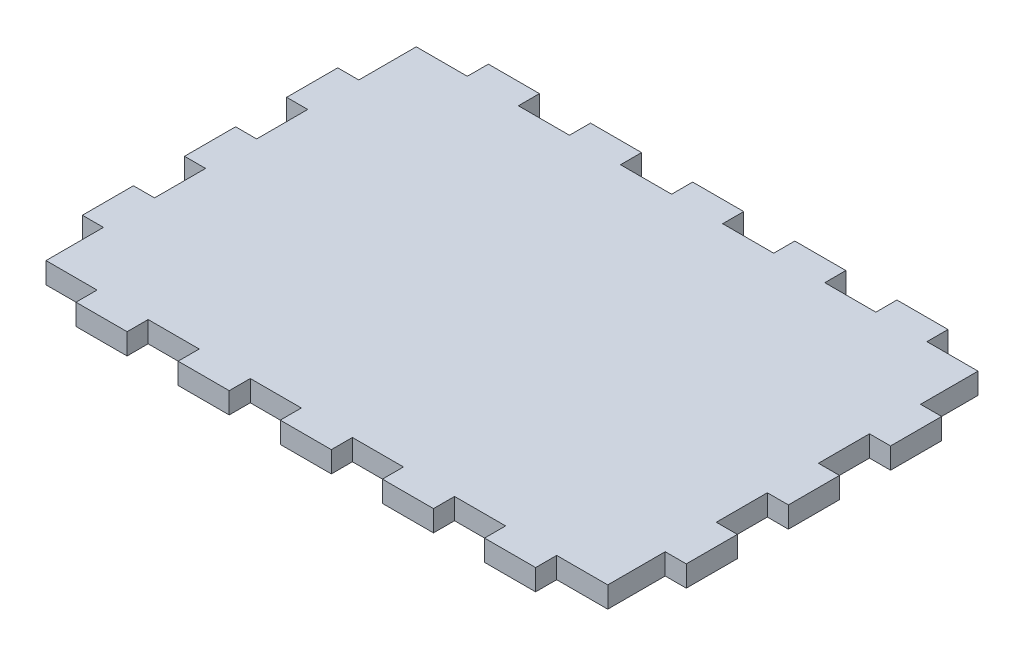
SolidWorks part; units mm, degrees
ref_plane "Plan de face" through (0, 0, 0) normal (0, 0, 1) x (1, 0, 0)
ref_plane "Plan de dessus" through (0, 0, 0) normal (0, 1, 0) x (1, 0, 0)
ref_plane "Plan de droite" through (0, 0, 0) normal (1, 0, 0) x (0, 0, -1)
sketch "Esquisse4" plane through (0, 0, 0) normal (0, 1, 0) x (1, 0, 0)
  line L1 (-44, 29) -> (44, 29)
  line L2 (-44, 29) -> (-44, -29)
  line L3 (-44, -29) -> (44, -29)
  line L4 (44, 29) -> (44, -29)
  line L5 (-44, 29) -> (44, -29) construction
  line L6 (-44, -29) -> (44, 29) construction
  point P0 (0, 0)
  dimension "D1" = 58
  dimension "D2" = 88
extrude "Boss.-Extru.3" add sketch "Esquisse4" along normal blind 3.3
sketch "Esquisse5" plane through (0, 0, 0) normal (0, -1, 0) x (1, 0, 0)
  line L0 (-44, 29) -> (44, 29) construction
  line L1 (4, 29) -> (-4, 29)
  line L2 (4, 29) -> (4, 32.3)
  line L3 (4, 32.3) -> (-4, 32.3)
  line L4 (-4, 29) -> (-4, 32.3)
  point P6 (0, 29)
  point P7 (0, 29)
  dimension "D1" = 3.3
  dimension "D2" = 8
extrude "Boss.-Extru.6" add sketch "Esquisse5" against normal blind 3.3
pattern_linear "Répétition linéaire2" count 3 spacing 16 along (-1, 0, 0) count 3 spacing 16 along (1, 0, 0) of "Boss.-Extru.6"
mirror "Symétrie1" about plane through (0, 0, 0) normal (0, 0, 1) of "Répétition linéaire2", "Boss.-Extru.6"
sketch "Esquisse6" plane through (0, 0, 0) normal (0, -1, 0) x (1, 0, 0)
  line L0 (-44, -29) -> (-44, 29) construction
  line L1 (-47.3, -4) -> (-44, -4)
  line L2 (-47.3, -4) -> (-47.3, 4)
  line L3 (-47.3, 4) -> (-44, 4)
  line L4 (-44, -4) -> (-44, 4)
  point P4 (-44, 0)
  point P7 (-44, 0)
  dimension "D1" = 8
  dimension "D2" = 3.3
extrude "Boss.-Extru.7" add sketch "Esquisse6" against normal blind 3.3
pattern_linear "Répétition linéaire3" count 2 spacing 16 along (0, 0, 1) count 2 spacing 16 along (0, 0, -1) of "Boss.-Extru.7"
mirror "Symétrie2" about plane through (0, 0, 0) normal (1, 0, 0) of "Répétition linéaire3", "Boss.-Extru.7"
